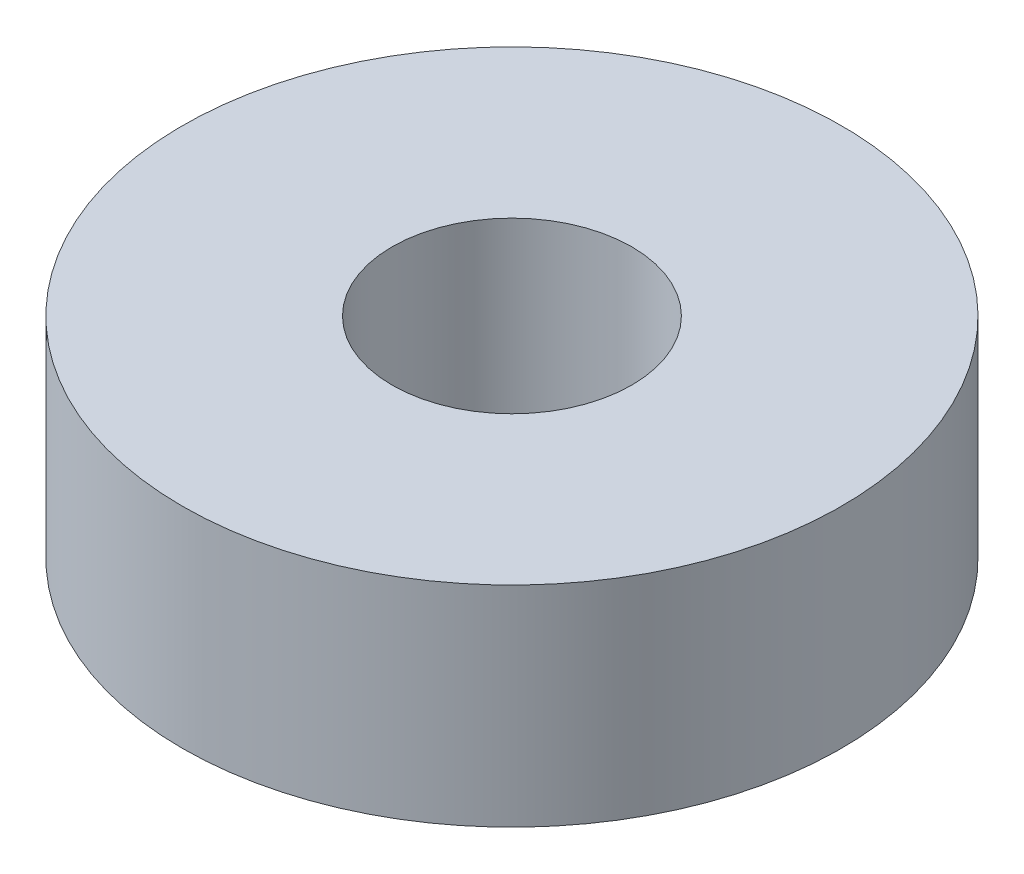
SolidWorks part; units mm, degrees
ref_plane "Front Plane" through (0, 0, 0) normal (0, 0, 1) x (1, 0, 0)
ref_plane "Top Plane" through (0, 0, 0) normal (0, 1, 0) x (1, 0, 0)
ref_plane "Right Plane" through (0, 0, 0) normal (1, 0, 0) x (0, 0, -1)
sketch "Sketch1" plane through (0, 0, 0) normal (0, 1, 0) x (1, 0, 0)
  circle A0 centre (0, 0) radius 11
  dimension "D1" = 22
extrude "Boss-Extrude1" add sketch "Sketch1" along normal blind 7 contours A0
sketch "Sketch2" plane through (0, 7, 0) normal (0, 1, 0) x (1, 0, 0)
  circle A0 centre (0, 0) radius 4
  dimension "D1" = 8
extrude "Cut-Extrude1" cut sketch "Sketch2" against normal through all
